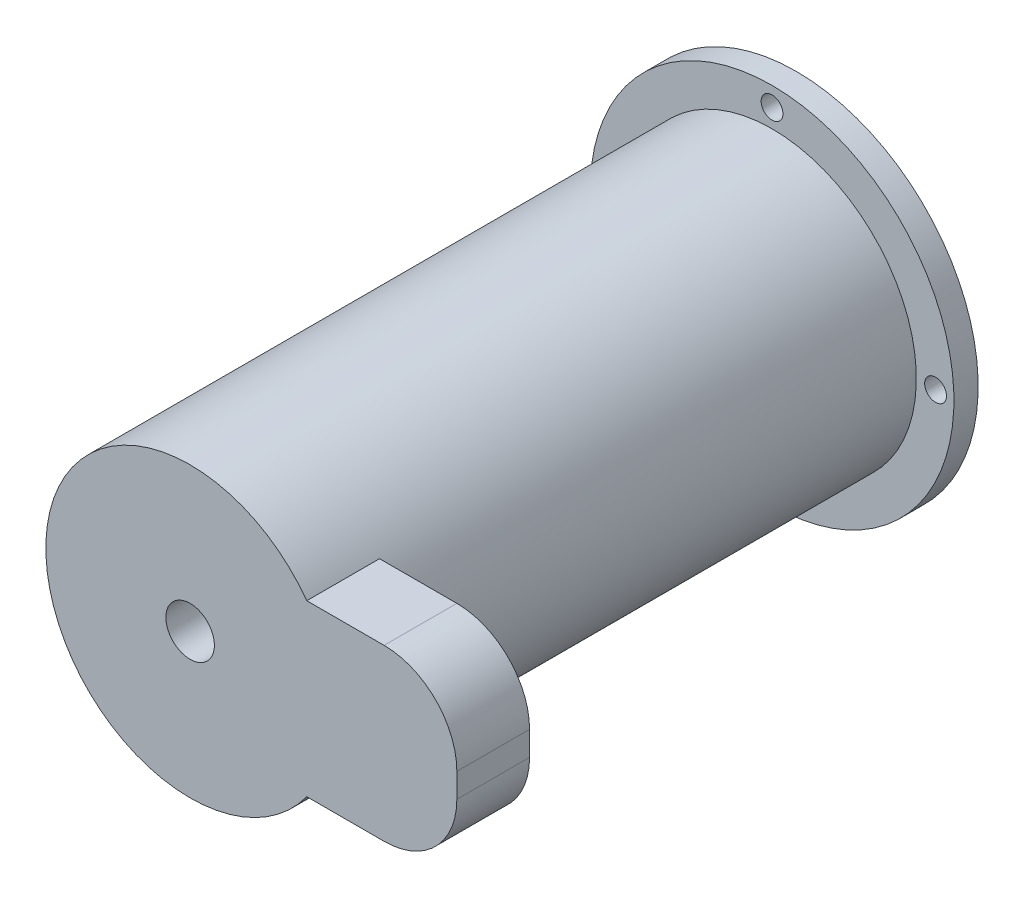
SolidWorks part; units mm, degrees
ref_plane "Front Plane" through (0, 0, 0) normal (0, 0, 1) x (1, 0, 0)
ref_plane "Top Plane" through (0, 0, 0) normal (0, 1, 0) x (1, 0, 0)
ref_plane "Right Plane" through (0, 0, 0) normal (1, 0, 0) x (0, 0, -1)
sketch "Sketch1" plane through (0, 0, 0) normal (0, 1, 0) x (1, 0, 0)
  circle A0 centre (0, 0) radius 75
  dimension "D1" = 150
extrude "Boss-Extrude1" add sketch "Sketch1" along normal blind 10
sketch "Sketch2" plane through (0, 10, 0) normal (0, 1, 0) x (1, 0, 0)
  circle A0 centre (0, 0) radius 59.5
  dimension "D1" = 119
extrude "Boss-Extrude2" add sketch "Sketch2" along normal blind 240
sketch "Sketch6" plane through (0, 250, 0) normal (0, 1, 0) x (1, 0, 0)
  line L1 (48.117, 35) -> (80, 35)
  line L2 (110, 5) -> (110, -5)
  line L3 (80, -35) -> (48.117, -35)
  arc A0 (48.117, 35) -> (48.117, -35) centre (0, 0) cw
  circle A1 centre (0, 0) radius 59.5 construction
  arc A2 (110, 5) -> (80, 35) centre (80, 5) ccw
  arc A3 (110, -5) -> (80, -35) centre (80, -5) cw
  point P10 (110, 35)
  point P13 (110, -35)
  dimension "D1" = 30
  dimension "D2" = 30
  dimension "D3" = 70
extrude "Boss-Extrude3" add sketch "Sketch6" against normal blind 30
sketch "Sketch7" plane through (0, 250, 0) normal (0, 1, 0) x (1, 0, 0)
  circle A0 centre (0, 0) radius 10
  dimension "D1" = 20
extrude "Cut-Extrude1" cut sketch "Sketch7" against normal blind 30
sketch "Sketch9" plane through (0, 10, 0) normal (0, 1, 0) x (1, 0, 0)
  line L0 (0, 0) -> (0, 75)
  line L1 (0, 0) -> (-75, 0)
  circle A0 centre (0, 0) radius 75 construction
  circle A1 centre (0, 67.0965) radius 4.5
  circle A2 centre (-67.4401, 0) radius 4.5
  dimension "D1" = 9
  dimension "D2" = 9
extrude "Cut-Extrude3" cut sketch "Sketch9" against normal up to surface (10 mm away) contours A2 | A1 up to face at (0, 0, 75)
mirror "Mirror2" about plane through (0, 0, 0) normal (0, 0, 1) of "Cut-Extrude3"
mirror "Mirror3" about plane through (0, 0, 0) normal (1, 0, 0) of "Cut-Extrude3"
sketch "Sketch10" plane through (0, 0, 0) normal (0, -1, 0) x (1, 0, 0)
  point P0 (0, 0)
move or copy body "Body-Move/Copy1" bodies to move or copy 109 copy no rotation origin (0, 0, 0) rotation axis (1, 0, 0) rotation angle 90
